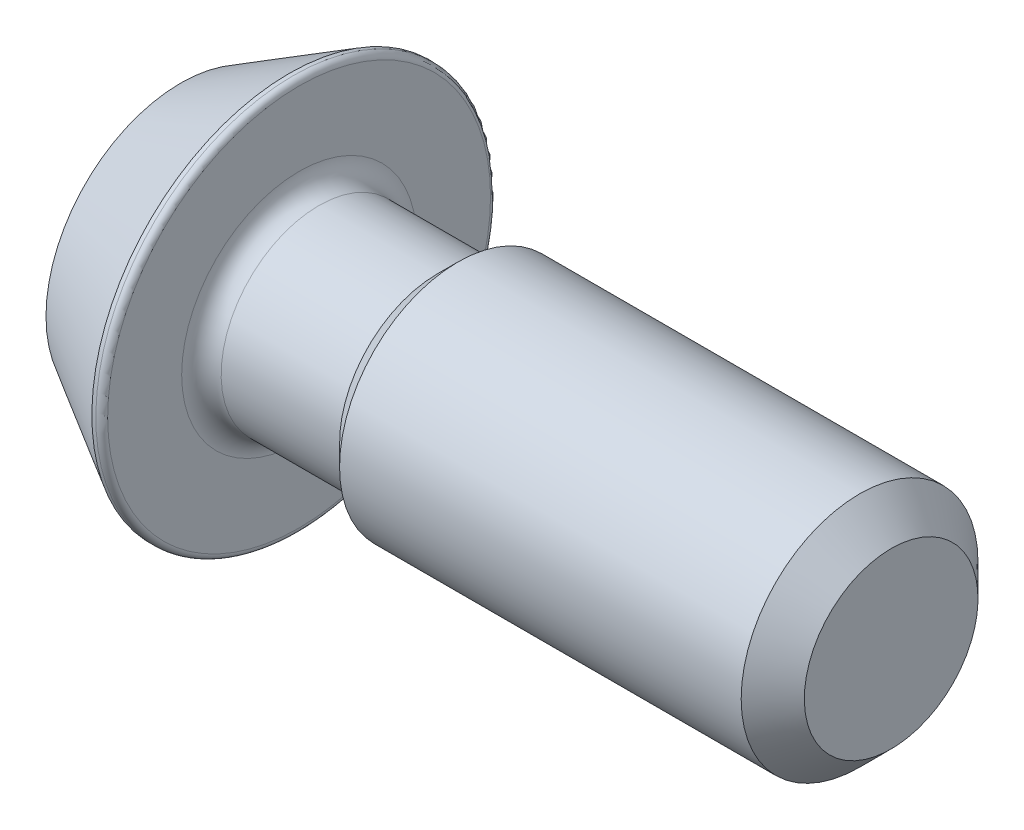
SolidWorks part; units mm, degrees
ref_plane "Спереди" through (0, 0, 0) normal (0, 0, 1) x (1, 0, 0)
ref_plane "Сверху" through (0, 0, 0) normal (0, 1, 0) x (1, 0, 0)
ref_plane "Справа" through (0, 0, 0) normal (1, 0, 0) x (0, 0, -1)
sketch "Эскиз1" plane through (0, 0, 0) normal (0, 0, 1) x (1, 0, 0)
  line L0 (0, 0) -> (0, 6.8246)
  line L1 (5.5, 10) -> (6, 10)
  line L2 (6, 10) -> (6, 4.95)
  line L4 (36, 6) -> (36, 0)
  line L5 (36, 0) -> (0, 0) construction
  line L6 (0, 0) -> (36, 0)
  line L7 (0, 6.8246) -> (5.5, 10)
  line L8 (6, 4.95) -> (13, 4.95)
  line L9 (13, 4.95) -> (14.05, 6)
  line L10 (14.05, 6) -> (36, 6)
  line L11 (0, 0) -> (-6.2497, 0) construction
  dimension "D4" = 36
  dimension "D1" = 0.5
  dimension "D2" = 12
  dimension "D3" = 20
  dimension "D5" = 6
  dimension "D6" = 30
  dimension "D7" = 7
  dimension "D8" = 45
  dimension "D9" = 9.9
revolve "Повернуть1" add sketch "Эскиз1" angle 360 about L5
cosmetic thread "Условное изображение резьбы1" parameters "D2"=10.072
sketch "Эскиз2" plane through (0, 0, 0) normal (-1, 0, 0) x (0, 0, 1)
  line L1 (1.7321, 3) -> (-1.7321, 3)
  line L2 (-1.7321, 3) -> (-3.4641, 0)
  line L3 (-3.4641, 0) -> (-1.7321, -3)
  line L4 (-1.7321, -3) -> (1.7321, -3)
  line L5 (1.7321, -3) -> (3.4641, 0)
  line L6 (3.4641, 0) -> (1.7321, 3)
  circle A0 centre (0, 0) radius 3 construction
  dimension "D1" = 6
extrude "Вырез-Вытянуть1" cut sketch "Эскиз2" against normal blind 4
fillet "Скругление1" radius 0.3 1 edges at (6, 10, 0)
chamfer "Фаска1" distance 1.6 angle 45 1 edges at (36, 6, 0)
fillet "Скругление2" radius 1 1 edges at (6, 4.95, 0)
